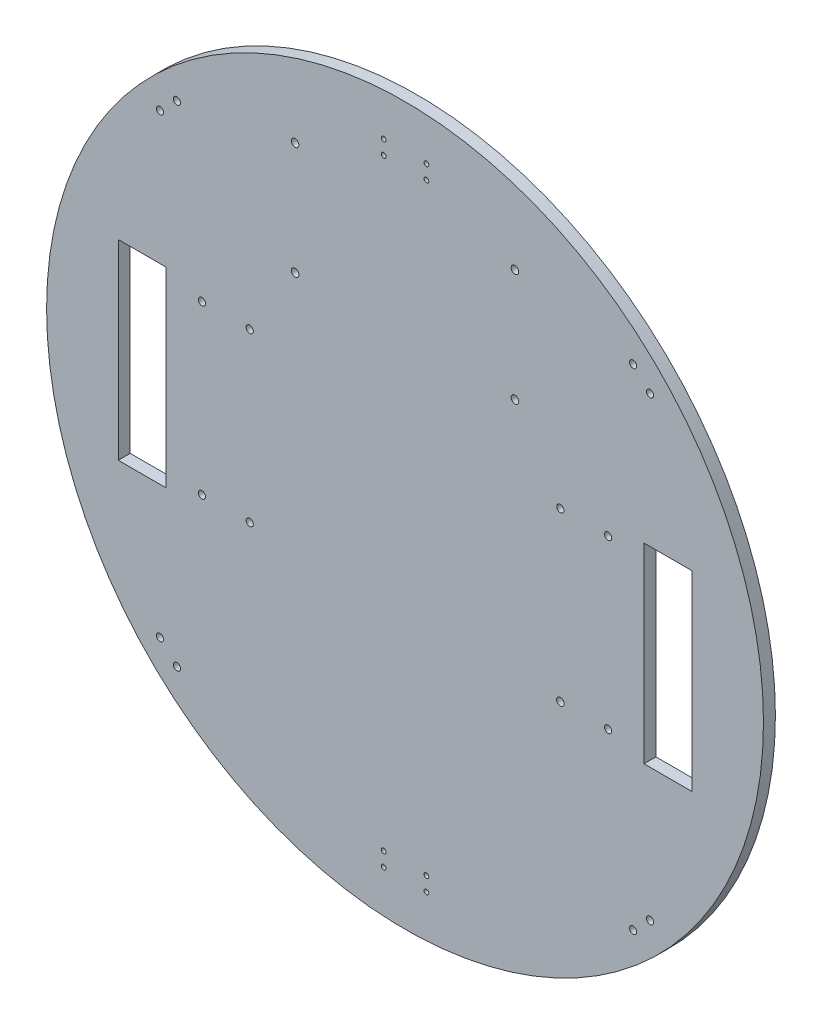
SolidWorks part; units mm, degrees
ref_plane "Plan de face" through (0, 0, 0) normal (0, 0, 1) x (1, 0, 0)
ref_plane "Plan de dessus" through (0, 0, 0) normal (0, 1, 0) x (1, 0, 0)
ref_plane "Plan de droite" through (0, 0, 0) normal (1, 0, 0) x (0, 0, -1)
sketch "Esquisse1" plane through (0, 0, 0) normal (0, 0, 1) x (1, 0, 0)
  circle A0 centre (0, 0) radius 150
extrude "base_circulaire" add sketch "Esquisse1" along normal blind 5
sketch "Esquisse2" plane through (0, 0, 5) normal (0, 0, 1) x (1, 0, 0)
  line L0 (-150, 0) -> (150, 0) construction
  line L2 (-120, 40) -> (-100, 40)
  line L3 (-120, 40) -> (-120, -40)
  line L4 (-120, -40) -> (-100, -40)
  line L5 (-100, 40) -> (-100, -40)
  line L6 (100, 40) -> (120, 40)
  line L7 (100, 40) -> (100, -40)
  line L8 (100, -40) -> (120, -40)
  line L9 (120, 40) -> (120, -40)
  circle A0 centre (0, 0) radius 150 construction
  dimension "D1" = 20
  dimension "D2" = 80
  dimension "D3" = 20
  dimension "D4" = 80
  dimension "D5" = 200
  dimension "D6" = 40
  dimension "D7" = 40
  dimension "D8" = 100
extrude "emplacement_roues" cut sketch "Esquisse2" against normal through all
sketch "Esquisse3" plane through (0, 0, 5) normal (0, 0, 1) x (1, 0, 0)
  line L0 (-150, 0) -> (150, 0) construction
  line L1 (-85, 123.5921) -> (-85, -123.5921) construction
  line L2 (85, -123.5921) -> (85, 123.5921) construction
  line L3 (85, -35) -> (-85, -35) construction
  line L4 (85, 35) -> (-85, 35) construction
  circle A0 centre (0, 0) radius 150 construction
  circle A1 centre (-85, 35) radius 1.5
  circle A2 centre (-85, -35) radius 1.5
  circle A3 centre (85, 35) radius 1.5
  circle A4 centre (85, -35) radius 1.5
  circle A5 centre (65, -35) radius 1.5755
  circle A6 centre (65, 35) radius 1.5
  circle A7 centre (-65, -35) radius 1.5
  circle A8 centre (-65, 35) radius 1.5
  dimension "D3" = 70
  dimension "D7" = 20
  dimension "D1" = 85
  dimension "D2" = 85
  dimension "D4" = 35
  dimension "D5" = 70
  dimension "D6" = 35
  dimension "D8" = 20
  dimension "D9" = 20
  dimension "D10" = 20
extrude "trous_fixation_mors" cut sketch "Esquisse3" against normal through all
sketch "Esquisse4" plane through (0, 0, 5) normal (0, 0, 1) x (1, 0, 0)
  line L0 (-150, 0) -> (150, 0) construction
  line L1 (0, 150) -> (0, -150) construction
  line L2 (0, 0) -> (-106.066, 106.066) construction
  line L3 (0, 0) -> (106.066, -106.066) construction
  line L4 (106.066, 106.066) -> (0, 0) construction
  line L5 (0, 0) -> (-106.066, -106.066) construction
  line L6 (121.1461, -76.8438) -> (76.5399, -121.45) construction
  line L7 (-76.1938, 121.7961) -> (-117.9982, 79.9917) construction
  line L8 (76.3094, 121.6805) -> (118.1138, 79.8761) construction
  line L9 (-115.3738, -82.6161) -> (-82.081, -115.9089) construction
  circle A0 centre (0, 0) radius 150 construction
  circle A1 centre (-102.5305, 95.4594) radius 1.5
  circle A2 centre (-95.4594, 102.5305) radius 1.5
  circle A3 centre (95.4594, 102.5305) radius 1.5
  circle A4 centre (102.5305, 95.4594) radius 1.5
  circle A5 centre (102.5305, -95.4594) radius 1.5
  circle A6 centre (95.4594, -102.5305) radius 1.5
  circle A7 centre (-95.4594, -102.5305) radius 1.5
  circle A8 centre (-102.5305, -95.4594) radius 1.5
  dimension "D9" = 140
  dimension "D1" = 45
  dimension "D2" = 45
  dimension "D3" = 45
  dimension "D4" = 90
  dimension "D5" = 140
  dimension "D6" = 90
  dimension "D7" = 90
  dimension "D8" = 90
  dimension "D10" = 140
  dimension "D11" = 140
  dimension "D12" = 10
  dimension "D13" = 5
  dimension "D14" = 5
  dimension "D15" = 10
  dimension "D16" = 5
  dimension "D17" = 10
  dimension "D18" = 5
  dimension "D19" = 10
extrude "trous fixation parois" cut sketch "Esquisse4" against normal through all
sketch "Esquisse5" plane through (0, 0, 5) normal (0, 0, 1) x (1, 0, 0)
  line L0 (0, -150) -> (0, 150) construction
  line L2 (15, -138) -> (-15, -138) construction
  line L3 (15, -138) -> (15, -120) construction
  line L4 (15, -120) -> (-15, -120) construction
  line L5 (-15, -138) -> (-15, -120) construction
  line L6 (15, 120) -> (-15, 120) construction
  line L7 (15, 120) -> (15, 138) construction
  line L8 (15, 138) -> (-15, 138) construction
  line L9 (-15, 120) -> (-15, 138) construction
  line L10 (8.947, -131.947) -> (-8.947, -131.947) construction
  line L11 (8.947, -131.947) -> (8.947, -126.053) construction
  line L12 (8.947, -126.053) -> (-8.947, -126.053) construction
  line L13 (-8.947, -131.947) -> (-8.947, -126.053) construction
  line L14 (8.947, 126.053) -> (-8.947, 126.053) construction
  line L15 (8.947, 126.053) -> (8.947, 131.947) construction
  line L16 (8.947, 131.947) -> (-8.947, 131.947) construction
  line L17 (-8.947, 126.053) -> (-8.947, 131.947) construction
  circle A0 centre (0, 0) radius 150 construction
  circle A1 centre (8.947, 126.053) radius 1
  circle A2 centre (8.947, 131.947) radius 1
  circle A3 centre (-8.947, 126.053) radius 1
  circle A4 centre (-8.947, 131.947) radius 1
  circle A5 centre (8.947, -131.947) radius 1
  circle A6 centre (-8.947, -131.947) radius 1
  circle A7 centre (8.947, -126.053) radius 1
  circle A8 centre (-8.947, -126.053) radius 1
  dimension "D1" = 30
  dimension "D2" = 18
  dimension "D3" = 15
  dimension "D4" = 30
  dimension "D5" = 18
  dimension "D6" = 15
  dimension "D7" = 120
  dimension "D8" = 120
  dimension "D9" = 6.053
  dimension "D10" = 6.053
  dimension "D11" = 6.053
  dimension "D12" = 6.053
  dimension "D13" = 6.053
  dimension "D14" = 6.053
  dimension "D15" = 6.053
  dimension "D16" = 6.053
extrude "trous fixation roues folles" cut sketch "Esquisse5" against normal through all
sketch "Esquisse6" plane through (0, 0, 5) normal (0, 0, 1) x (1, 0, 0)
  line L1 (46.005, 65) -> (-46.005, 65) construction
  line L2 (46.005, 65) -> (46.005, 112.01) construction
  line L3 (46.005, 112.01) -> (-46.005, 112.01) construction
  line L4 (-46.005, 65) -> (-46.005, 112.01) construction
  circle A0 centre (46.005, 65) radius 1.59
  circle A1 centre (46.005, 112.01) radius 1.59
  circle A2 centre (-46.005, 65) radius 1.59
  circle A3 centre (-46.005, 112.01) radius 1.59
  dimension "D3" = 46.005
  dimension "D1" = 92.01
  dimension "D2" = 47.01
  dimension "D4" = 65
extrude "trous fixation carte open UPS" cut sketch "Esquisse6" against normal through all
